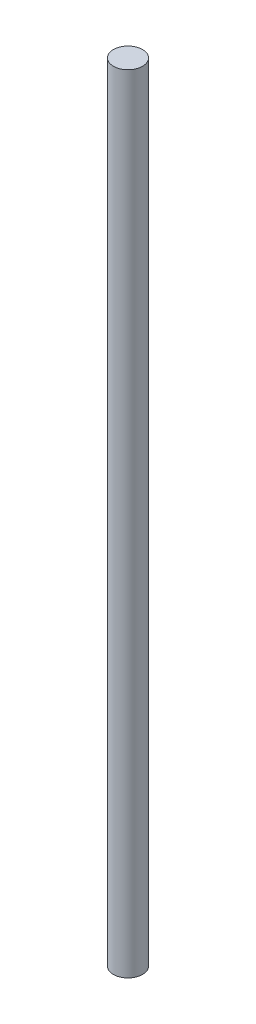
SolidWorks part; units mm, degrees
ref_plane "Front Plane" through (0, 0, 0) normal (0, 0, 1) x (1, 0, 0)
ref_plane "Top Plane" through (0, 0, 0) normal (0, 1, 0) x (1, 0, 0)
ref_plane "Right Plane" through (0, 0, 0) normal (1, 0, 0) x (0, 0, -1)
sketch "Sketch1" plane through (0, 0, 0) normal (0, 1, 0) x (1, 0, 0)
  circle A0 centre (0, 0) radius 4.9
  dimension "D1" = 9.8
extrude "Boss-Extrude1" add sketch "Sketch1" along normal blind 265
